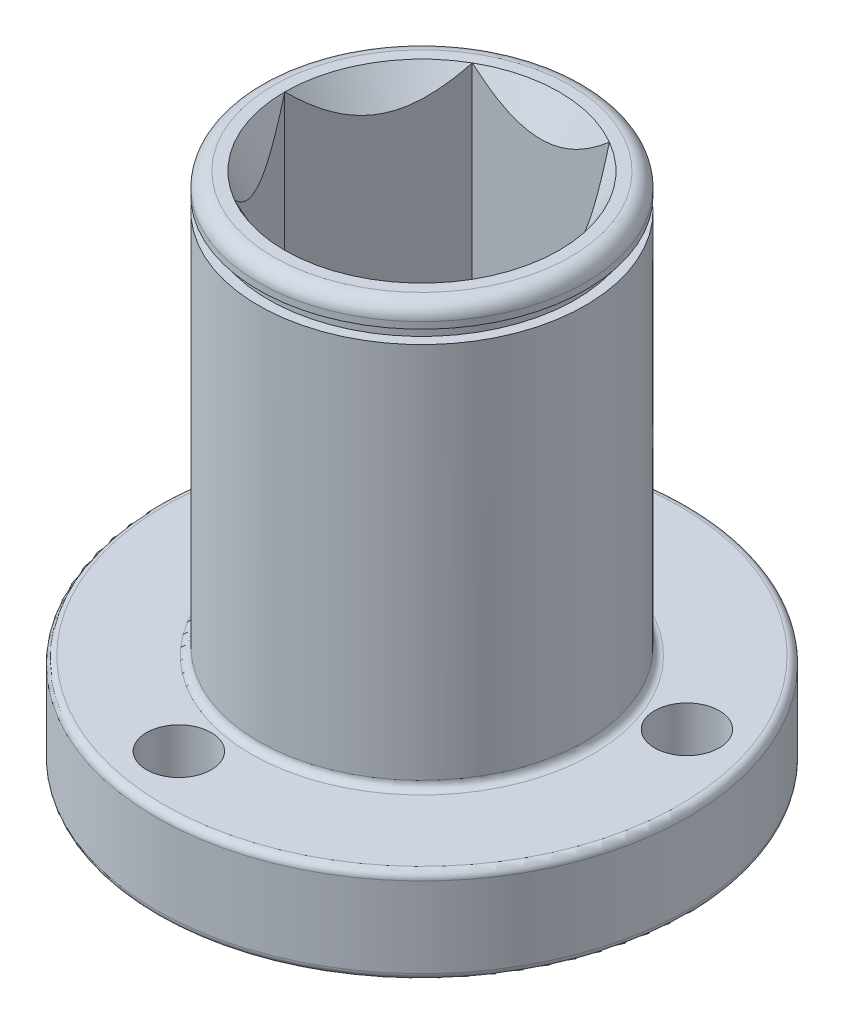
SolidWorks part; units mm, degrees
ref_plane "Front" through (0, 0, 0) normal (0, 0, 1) x (1, 0, 0)
ref_plane "Top" through (0, 0, 0) normal (0, 1, 0) x (1, 0, 0)
ref_plane "Right" through (0, 0, 0) normal (1, 0, 0) x (0, 0, -1)
sketch "Sketch2" plane through (0, 0, 0) normal (0, 1, 0) x (1, 0, 0)
  circle A0 centre (0, 0) radius 28.3845
  dimension "D1" = 56.769
extrude "Boss-Extrude1" add sketch "Sketch2" along normal blind 10.16
sketch "Sketch3" plane through (0, 10.16, 0) normal (0, 1, 0) x (1, 0, 0)
  circle A0 centre (0, 0) radius 17.4625
  dimension "D1" = 34.925
extrude "Boss-Extrude2" add sketch "Sketch3" along normal blind 44.831
sketch "Sketch4" plane through (0, 54.991, 0) normal (0, 1, 0) x (1, 0, 0)
  line L1 (14.6647, 0) -> (7.3323, 12.7)
  line L2 (7.3323, 12.7) -> (-7.3323, 12.7)
  line L3 (-7.3323, 12.7) -> (-14.6647, 0)
  line L4 (-14.6647, 0) -> (-7.3323, -12.7)
  line L5 (-7.3323, -12.7) -> (7.3323, -12.7)
  line L6 (7.3323, -12.7) -> (14.6647, 0)
  circle A0 centre (0, 0) radius 12.7 construction
  dimension "D1" = 25.4
extrude "Cut-Extrude1" cut sketch "Sketch4" against normal through all both and the other way through all
hole_wizard "5/16-24 Tapped Hole2" positions "Sketch8" profile "Sketch9" tap size "5/16-24" standard "ANSI Inch" end condition through all
sketch "Sketch8" plane through (0, 0, 0) normal (0, -1, 0) x (-1, 0, 0)
  line L1 (4.1386, -21.8363) -> (16.8415, 14.5022) construction
  line L2 (16.8415, 14.5022) -> (-20.9801, 7.334) construction
  line L3 (-20.9801, 7.334) -> (4.1386, -21.8363) construction
  circle A0 centre (0, 0) radius 22.225 construction
  point P3 (4.1386, -21.8363)
  point P4 (16.8415, 14.5022)
  point P5 (-20.9801, 7.334)
  dimension "D1" = 44.45
sketch "Sketch9" plane through (-4.1386, 0, 21.8363) normal (1, 0, 0) x (0, 0, -1)
  line L0 (0, 0) -> (0, 54.991)
  line L1 (0, 54.991) -> (3.4544, 54.991)
  line L2 (3.4544, 54.991) -> (3.4544, 0)
  line L5 (3.4544, 0) -> (0, 0)
  line L11 (0, -6.35) -> (0, 107.95) construction
  dimension "Thru Tap Drill Dia." = 6.9088
  dimension "Thru Tap Drill Depth" = 54.991
cosmetic thread "Hole Thread4" parameters "D2"=7.9375
cosmetic thread "Hole Thread5" parameters "D2"=7.9375
cosmetic thread "Hole Thread6" parameters "D2"=7.9375
sketch "Sketch10" plane through (0, 0, 0) normal (0, 0, 1) x (1, 0, 0)
  line L0 (14.6647, 54.991) -> (0, 29.591)
  line L1 (0, 0) -> (0, 9.9896) construction
  line L2 (14.6647, 54.991) -> (0, 54.991)
  line L3 (0, 54.991) -> (0, 29.591)
  line L4 (14.6647, 0) -> (0, 14.6647)
  line L5 (14.6647, 0) -> (0, 0)
  line L6 (0, 0) -> (0, 14.6647)
  line L7 (17.4625, 52.705) -> (16.3957, 52.705)
  line L8 (17.4625, 10.16) -> (17.4625, 54.991) construction
  line L9 (16.3957, 52.705) -> (16.3957, 51.2826)
  line L10 (16.3957, 51.2826) -> (17.4625, 51.2826)
  line L11 (17.4625, 52.705) -> (17.4625, 51.2826)
  line L12 (17.4625, 54.991) -> (-17.4625, 54.991) construction
  dimension "D1" = 30
  dimension "D2" = 45
  dimension "D3" = 2.286
  dimension "D4" = 32.7914
  dimension "D5" = 1.4224
revolve "Cut-Revolve1" cut sketch "Sketch10" angle 360 about L1
fillet "Fillet1" radius 1.5875 1 edges at (0, 54.991, 17.4625)
fillet "Fillet2" radius 0.7937 3 edges at (0, 10.16, 17.4625) (0, 10.16, 28.3845) (0, 0, 28.3845)
